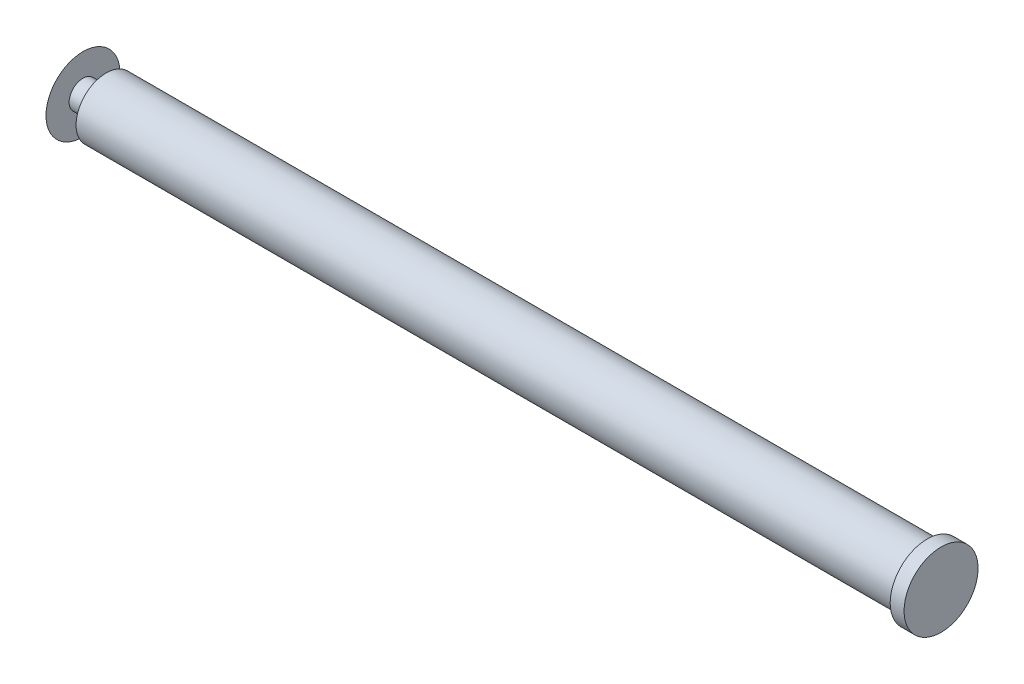
SolidWorks part; units mm, degrees
material "1.0050 (E295)"
ref_plane "Front Plane" through (0, 0, 0) normal (0, 0, 1) x (1, 0, 0)
ref_plane "Top Plane" through (0, 0, 0) normal (0, 1, 0) x (1, 0, 0)
ref_plane "Right Plane" through (0, 0, 0) normal (1, 0, 0) x (0, 0, -1)
sketch "Sketch1" plane through (0, 0, 0) normal (0, 0, 1) x (1, 0, 0)
  line L0 (-129.8121, 0) -> (134.4096, 0) construction
  line L1 (247.1948, 0) -> (-247.1948, 0) construction
  line L2 (319.6329, 0) -> (319.6329, 16)
  line L3 (319.6329, 16) -> (313.6329, 16)
  line L4 (313.6329, 16) -> (313.6329, 13)
  line L5 (313.6329, 13) -> (-41.3671, 13)
  line L6 (-41.3671, 13) -> (-41.3671, 6)
  line L7 (-41.3671, 6) -> (-51.3671, 6)
  line L8 (-51.3671, 6) -> (-51.3671, 16)
  line L9 (-55.3671, 0) -> (319.6329, 0)
  arc A0 (-51.3671, 16) -> (-55.3671, 0) centre (-21.3671, 0) ccw
  dimension "D11" = 34
  dimension "D1" = 6
  dimension "D2" = 4
  dimension "D3" = 13
  dimension "D4" = 16
  dimension "D5" = 10
  dimension "D6" = 16
  dimension "D7" = 6
  dimension "D8" = 375
  dimension "D9" = 7
  dimension "D10" = 10
  dimension "D12" = 3
revolve "Revolve1" add sketch "Sketch1" angle 360 about L0
